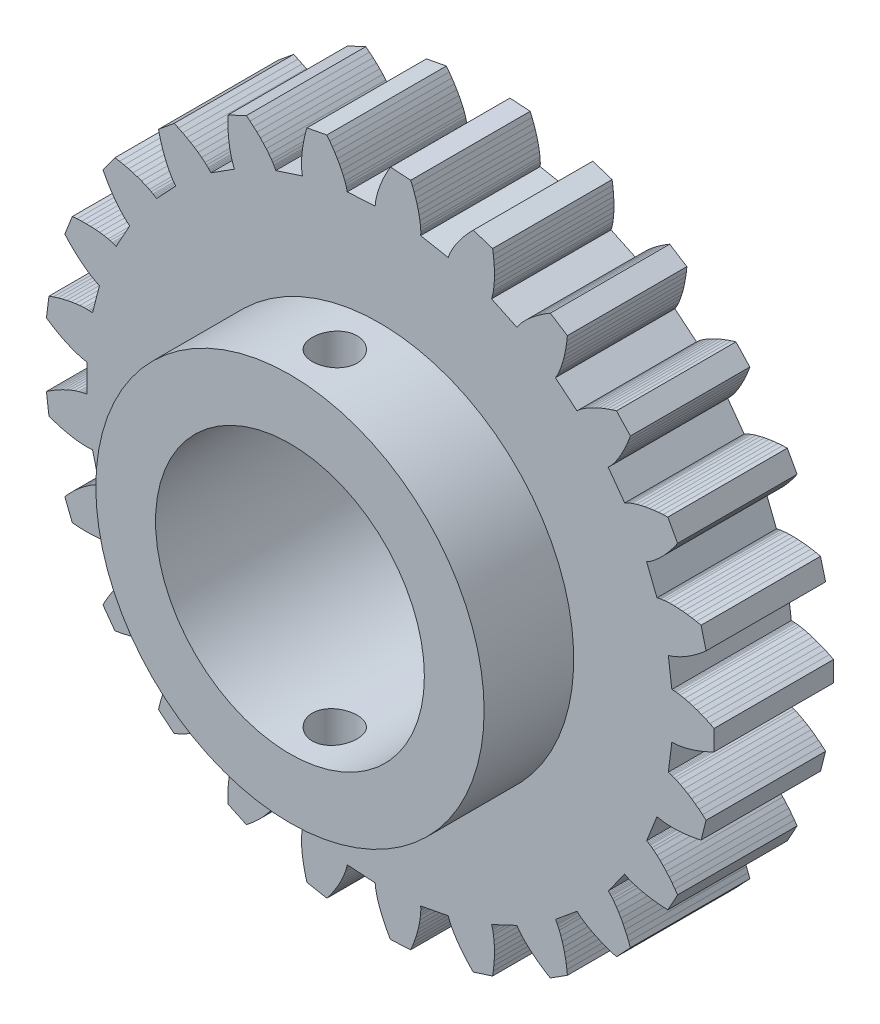
SolidWorks part; units mm, degrees
ref_plane "Front Plane" through (0, 0, 0) normal (0, 0, 1) x (1, 0, 0)
ref_plane "Top Plane" through (0, 0, 0) normal (0, 1, 0) x (1, 0, 0)
ref_plane "Right Plane" through (0, 0, 0) normal (1, 0, 0) x (0, 0, -1)
sketch "Model" plane through (0, 0, 0) normal (0, 0, 1) x (1, 0, 0)
  line L0 (22.5153, 13.4937) -> (22.5501, 13.4944)
  line L1 (22.5501, 13.4944) -> (22.5851, 13.4936)
  line L2 (22.5851, 13.4936) -> (22.6201, 13.4916)
  line L3 (22.6201, 13.4916) -> (22.6552, 13.4888)
  line L4 (22.6552, 13.4888) -> (22.7255, 13.481)
  line L5 (22.7255, 13.481) -> (22.796, 13.4706)
  line L6 (22.796, 13.4706) -> (22.9373, 13.4433)
  line L7 (22.9373, 13.4433) -> (23.079, 13.4085)
  line L8 (23.079, 13.4085) -> (23.221, 13.3669)
  line L9 (23.221, 13.3669) -> (23.363, 13.3191)
  line L10 (23.363, 13.3191) -> (23.5051, 13.2655)
  line L11 (23.5051, 13.2655) -> (23.647, 13.2062)
  line L12 (23.647, 13.2062) -> (23.7888, 13.1416)
  line L13 (23.7888, 13.1416) -> (23.9303, 13.0718)
  line L14 (23.9303, 13.0718) -> (23.9303, 12.3915)
  line L15 (23.9303, 12.3915) -> (23.7888, 12.3217)
  line L16 (23.7888, 12.3217) -> (23.647, 12.257)
  line L17 (23.647, 12.257) -> (23.5051, 12.1978)
  line L18 (23.5051, 12.1978) -> (23.363, 12.1441)
  line L19 (23.363, 12.1441) -> (23.221, 12.0963)
  line L20 (23.221, 12.0963) -> (23.079, 12.0548)
  line L21 (23.079, 12.0548) -> (22.9373, 12.0199)
  line L22 (22.9373, 12.0199) -> (22.796, 11.9927)
  line L23 (22.796, 11.9927) -> (22.7255, 11.9823)
  line L24 (22.7255, 11.9823) -> (22.6552, 11.9745)
  line L25 (22.6552, 11.9745) -> (22.6201, 11.9716)
  line L26 (22.6201, 11.9716) -> (22.5851, 11.9697)
  line L27 (22.5851, 11.9697) -> (22.5501, 11.9688)
  line L28 (22.5501, 11.9688) -> (22.5153, 11.9696)
  line L29 (22.5153, 11.9696) -> (22.3975, 11.0367)
  line L30 (22.3975, 11.0367) -> (22.4314, 11.0287)
  line L31 (22.4314, 11.0287) -> (22.465, 11.0192)
  line L32 (22.465, 11.0192) -> (22.4984, 11.0086)
  line L33 (22.4984, 11.0086) -> (22.5317, 10.9971)
  line L34 (22.5317, 10.9971) -> (22.5978, 10.9721)
  line L35 (22.5978, 10.9721) -> (22.6635, 10.9445)
  line L36 (22.6635, 10.9445) -> (22.7937, 10.8829)
  line L37 (22.7937, 10.8829) -> (22.9223, 10.8139)
  line L38 (22.9223, 10.8139) -> (23.0494, 10.7384)
  line L39 (23.0494, 10.7384) -> (23.1751, 10.6567)
  line L40 (23.1751, 10.6567) -> (23.2994, 10.5694)
  line L41 (23.2994, 10.5694) -> (23.4221, 10.4767)
  line L42 (23.4221, 10.4767) -> (23.5434, 10.3789)
  line L43 (23.5434, 10.3789) -> (23.6631, 10.2761)
  line L44 (23.6631, 10.2761) -> (23.4939, 9.6172)
  line L45 (23.4939, 9.6172) -> (23.3395, 9.5847)
  line L46 (23.3395, 9.5847) -> (23.1861, 9.5574)
  line L47 (23.1861, 9.5574) -> (23.0339, 9.5353)
  line L48 (23.0339, 9.5353) -> (22.8829, 9.5187)
  line L49 (22.8829, 9.5187) -> (22.7334, 9.5077)
  line L50 (22.7334, 9.5077) -> (22.5856, 9.5027)
  line L51 (22.5856, 9.5027) -> (22.4397, 9.5042)
  line L52 (22.4397, 9.5042) -> (22.296, 9.513)
  line L53 (22.296, 9.513) -> (22.2251, 9.5205)
  line L54 (22.2251, 9.5205) -> (22.1551, 9.5304)
  line L55 (22.1551, 9.5304) -> (22.1204, 9.5364)
  line L56 (22.1204, 9.5364) -> (22.086, 9.5432)
  line L57 (22.086, 9.5432) -> (22.0519, 9.551)
  line L58 (22.0519, 9.551) -> (22.0184, 9.5604)
  line L59 (22.0184, 9.5604) -> (21.6723, 8.6861)
  line L60 (21.6723, 8.6861) -> (21.7031, 8.67)
  line L61 (21.7031, 8.67) -> (21.7333, 8.6524)
  line L62 (21.7333, 8.6524) -> (21.7631, 8.6338)
  line L63 (21.7631, 8.6338) -> (21.7925, 8.6145)
  line L64 (21.7925, 8.6145) -> (21.8503, 8.5737)
  line L65 (21.8503, 8.5737) -> (21.9071, 8.5306)
  line L66 (21.9071, 8.5306) -> (22.0178, 8.4387)
  line L67 (22.0178, 8.4387) -> (22.1252, 8.3399)
  line L68 (22.1252, 8.3399) -> (22.2296, 8.2351)
  line L69 (22.2296, 8.2351) -> (22.331, 8.1247)
  line L70 (22.331, 8.1247) -> (22.4297, 8.0093)
  line L71 (22.4297, 8.0093) -> (22.5255, 7.889)
  line L72 (22.5255, 7.889) -> (22.6186, 7.764)
  line L73 (22.6186, 7.764) -> (22.709, 7.6347)
  line L74 (22.709, 7.6347) -> (22.3812, 7.0385)
  line L75 (22.3812, 7.0385) -> (22.2236, 7.0455)
  line L76 (22.2236, 7.0455) -> (22.0683, 7.0572)
  line L77 (22.0683, 7.0572) -> (21.9153, 7.0737)
  line L78 (21.9153, 7.0737) -> (21.765, 7.0951)
  line L79 (21.765, 7.0951) -> (21.6175, 7.1216)
  line L80 (21.6175, 7.1216) -> (21.473, 7.1536)
  line L81 (21.473, 7.1536) -> (21.3321, 7.1913)
  line L82 (21.3321, 7.1913) -> (21.1951, 7.2356)
  line L83 (21.1951, 7.2356) -> (21.1283, 7.2604)
  line L84 (21.1283, 7.2604) -> (21.0629, 7.2874)
  line L85 (21.0629, 7.2874) -> (21.0308, 7.3018)
  line L86 (21.0308, 7.3018) -> (20.9992, 7.317)
  line L87 (20.9992, 7.317) -> (20.9681, 7.3331)
  line L88 (20.9681, 7.3331) -> (20.938, 7.3505)
  line L89 (20.938, 7.3505) -> (20.3853, 6.5898)
  line L90 (20.3853, 6.5898) -> (20.4112, 6.5665)
  line L91 (20.4112, 6.5665) -> (20.4361, 6.5419)
  line L92 (20.4361, 6.5419) -> (20.4602, 6.5165)
  line L93 (20.4602, 6.5165) -> (20.4839, 6.4905)
  line L94 (20.4839, 6.4905) -> (20.5298, 6.4366)
  line L95 (20.5298, 6.4366) -> (20.574, 6.3808)
  line L96 (20.574, 6.3808) -> (20.6584, 6.2642)
  line L97 (20.6584, 6.2642) -> (20.7379, 6.1418)
  line L98 (20.7379, 6.1418) -> (20.8129, 6.0143)
  line L99 (20.8129, 6.0143) -> (20.8838, 5.8822)
  line L100 (20.8838, 5.8822) -> (20.9506, 5.7458)
  line L101 (20.9506, 5.7458) -> (21.0135, 5.6055)
  line L102 (21.0135, 5.6055) -> (21.0726, 5.4613)
  line L103 (21.0726, 5.4613) -> (21.128, 5.3136)
  line L104 (21.128, 5.3136) -> (20.6622, 4.8176)
  line L105 (20.6622, 4.8176) -> (20.5113, 4.8636)
  line L106 (20.5113, 4.8636) -> (20.3638, 4.9136)
  line L107 (20.3638, 4.9136) -> (20.2197, 4.9675)
  line L108 (20.2197, 4.9675) -> (20.0794, 5.0257)
  line L109 (20.0794, 5.0257) -> (19.9432, 5.0881)
  line L110 (19.9432, 5.0881) -> (19.8112, 5.1549)
  line L111 (19.8112, 5.1549) -> (19.6841, 5.2265)
  line L112 (19.6841, 5.2265) -> (19.5624, 5.3035)
  line L113 (19.5624, 5.3035) -> (19.5039, 5.3441)
  line L114 (19.5039, 5.3441) -> (19.4472, 5.3866)
  line L115 (19.4472, 5.3866) -> (19.4197, 5.4085)
  line L116 (19.4197, 5.4085) -> (19.3929, 5.4311)
  line L117 (19.3929, 5.4311) -> (19.3668, 5.4543)
  line L118 (19.3668, 5.4543) -> (19.3419, 5.4787)
  line L119 (19.3419, 5.4787) -> (18.6174, 4.8793)
  line L120 (18.6174, 4.8793) -> (18.6367, 4.8503)
  line L121 (18.6367, 4.8503) -> (18.6547, 4.8204)
  line L122 (18.6547, 4.8204) -> (18.6718, 4.7898)
  line L123 (18.6718, 4.7898) -> (18.6882, 4.7586)
  line L124 (18.6882, 4.7586) -> (18.7193, 4.6951)
  line L125 (18.7193, 4.6951) -> (18.7483, 4.63)
  line L126 (18.7483, 4.63) -> (18.801, 4.496)
  line L127 (18.801, 4.496) -> (18.8476, 4.3577)
  line L128 (18.8476, 4.3577) -> (18.8885, 4.2156)
  line L129 (18.8885, 4.2156) -> (18.9243, 4.07)
  line L130 (18.9243, 4.07) -> (18.9551, 3.9213)
  line L131 (18.9551, 3.9213) -> (18.9811, 3.7697)
  line L132 (18.9811, 3.7697) -> (19.0025, 3.6154)
  line L133 (19.0025, 3.6154) -> (19.0194, 3.4586)
  line L134 (19.0194, 3.4586) -> (18.445, 3.094)
  line L135 (18.445, 3.094) -> (18.3102, 3.1761)
  line L136 (18.3102, 3.1761) -> (18.1797, 3.2611)
  line L137 (18.1797, 3.2611) -> (18.0536, 3.3493)
  line L138 (18.0536, 3.3493) -> (17.9322, 3.4404)
  line L139 (17.9322, 3.4404) -> (17.8157, 3.5348)
  line L140 (17.8157, 3.5348) -> (17.7045, 3.6323)
  line L141 (17.7045, 3.6323) -> (17.5992, 3.7333)
  line L142 (17.5992, 3.7333) -> (17.5004, 3.8381)
  line L143 (17.5004, 3.8381) -> (17.4539, 3.892)
  line L144 (17.4539, 3.892) -> (17.4096, 3.9472)
  line L145 (17.4096, 3.9472) -> (17.3884, 3.9753)
  line L146 (17.3884, 3.9753) -> (17.368, 4.0038)
  line L147 (17.368, 4.0038) -> (17.3486, 4.0329)
  line L148 (17.3486, 4.0329) -> (17.3305, 4.0626)
  line L149 (17.3305, 4.0626) -> (16.4797, 3.6623)
  line L150 (16.4797, 3.6623) -> (16.4912, 3.6294)
  line L151 (16.4912, 3.6294) -> (16.5012, 3.5959)
  line L152 (16.5012, 3.5959) -> (16.5101, 3.562)
  line L153 (16.5101, 3.562) -> (16.5183, 3.5278)
  line L154 (16.5183, 3.5278) -> (16.5326, 3.4585)
  line L155 (16.5326, 3.4585) -> (16.5445, 3.3882)
  line L156 (16.5445, 3.3882) -> (16.5622, 3.2454)
  line L157 (16.5622, 3.2454) -> (16.5729, 3.0998)
  line L158 (16.5729, 3.0998) -> (16.5772, 2.952)
  line L159 (16.5772, 2.952) -> (16.5756, 2.8021)
  line L160 (16.5756, 2.8021) -> (16.5685, 2.6504)
  line L161 (16.5685, 2.6504) -> (16.556, 2.4971)
  line L162 (16.556, 2.4971) -> (16.5384, 2.3423)
  line L163 (16.5384, 2.3423) -> (16.5157, 2.1862)
  line L164 (16.5157, 2.1862) -> (15.8687, 1.9759)
  line L165 (15.8687, 1.9759) -> (15.7586, 2.0889)
  line L166 (15.7586, 2.0889) -> (15.6533, 2.2038)
  line L167 (15.6533, 2.2038) -> (15.5531, 2.3205)
  line L168 (15.5531, 2.3205) -> (15.4582, 2.439)
  line L169 (15.4582, 2.439) -> (15.3688, 2.5593)
  line L170 (15.3688, 2.5593) -> (15.2854, 2.6815)
  line L171 (15.2854, 2.6815) -> (15.2085, 2.8055)
  line L172 (15.2085, 2.8055) -> (15.1389, 2.9315)
  line L173 (15.1389, 2.9315) -> (15.1072, 2.9954)
  line L174 (15.1072, 2.9954) -> (15.078, 3.0598)
  line L175 (15.078, 3.0598) -> (15.0645, 3.0923)
  line L176 (15.0645, 3.0923) -> (15.0519, 3.125)
  line L177 (15.0519, 3.125) -> (15.0402, 3.158)
  line L178 (15.0402, 3.158) -> (15.0302, 3.1913)
  line L179 (15.0302, 3.1913) -> (14.1065, 3.0151)
  line L180 (14.1065, 3.0151) -> (14.1095, 2.9804)
  line L181 (14.1095, 2.9804) -> (14.1108, 2.9455)
  line L182 (14.1108, 2.9455) -> (14.111, 2.9104)
  line L183 (14.111, 2.9104) -> (14.1104, 2.8752)
  line L184 (14.1104, 2.8752) -> (14.107, 2.8046)
  line L185 (14.107, 2.8046) -> (14.1011, 2.7336)
  line L186 (14.1011, 2.7336) -> (14.0827, 2.5908)
  line L187 (14.0827, 2.5908) -> (14.0569, 2.4471)
  line L188 (14.0569, 2.4471) -> (14.0243, 2.3029)
  line L189 (14.0243, 2.3029) -> (13.9855, 2.1581)
  line L190 (13.9855, 2.1581) -> (13.9409, 2.0129)
  line L191 (13.9409, 2.0129) -> (13.8907, 1.8675)
  line L192 (13.8907, 1.8675) -> (13.8351, 1.722)
  line L193 (13.8351, 1.722) -> (13.7743, 1.5764)
  line L194 (13.7743, 1.5764) -> (13.0953, 1.5337)
  line L195 (13.0953, 1.5337) -> (13.0168, 1.6705)
  line L196 (13.0168, 1.6705) -> (12.9434, 1.808)
  line L197 (12.9434, 1.808) -> (12.8753, 1.9459)
  line L198 (12.8753, 1.9459) -> (12.8128, 2.0843)
  line L199 (12.8128, 2.0843) -> (12.7562, 2.2231)
  line L200 (12.7562, 2.2231) -> (12.7058, 2.3621)
  line L201 (12.7058, 2.3621) -> (12.6622, 2.5014)
  line L202 (12.6622, 2.5014) -> (12.6261, 2.6408)
  line L203 (12.6261, 2.6408) -> (12.6113, 2.7105)
  line L204 (12.6113, 2.7105) -> (12.599, 2.7801)
  line L205 (12.599, 2.7801) -> (12.594, 2.815)
  line L206 (12.594, 2.815) -> (12.5899, 2.8498)
  line L207 (12.5899, 2.8498) -> (12.5868, 2.8846)
  line L208 (12.5868, 2.8846) -> (12.5854, 2.9194)
  line L209 (12.5854, 2.9194) -> (11.6469, 2.9784)
  line L210 (11.6469, 2.9784) -> (11.6411, 2.9441)
  line L211 (11.6411, 2.9441) -> (11.6337, 2.91)
  line L212 (11.6337, 2.91) -> (11.6253, 2.8759)
  line L213 (11.6253, 2.8759) -> (11.6159, 2.842)
  line L214 (11.6159, 2.842) -> (11.595, 2.7744)
  line L215 (11.595, 2.7744) -> (11.5716, 2.7071)
  line L216 (11.5716, 2.7071) -> (11.5184, 2.5733)
  line L217 (11.5184, 2.5733) -> (11.4576, 2.4407)
  line L218 (11.4576, 2.4407) -> (11.3902, 2.309)
  line L219 (11.3902, 2.309) -> (11.3166, 2.1784)
  line L220 (11.3166, 2.1784) -> (11.2372, 2.049)
  line L221 (11.2372, 2.049) -> (11.1525, 1.9206)
  line L222 (11.1525, 1.9206) -> (11.0624, 1.7935)
  line L223 (11.0624, 1.7935) -> (10.9673, 1.6676)
  line L224 (10.9673, 1.6676) -> (10.2991, 1.7951)
  line L225 (10.2991, 1.7951) -> (10.257, 1.9471)
  line L226 (10.257, 1.9471) -> (10.2201, 2.0985)
  line L227 (10.2201, 2.0985) -> (10.1885, 2.249)
  line L228 (10.1885, 2.249) -> (10.1624, 2.3986)
  line L229 (10.1624, 2.3986) -> (10.1421, 2.5471)
  line L230 (10.1421, 2.5471) -> (10.1278, 2.6943)
  line L231 (10.1278, 2.6943) -> (10.1202, 2.8401)
  line L232 (10.1202, 2.8401) -> (10.1199, 2.984)
  line L233 (10.1199, 2.984) -> (10.1229, 3.0552)
  line L234 (10.1229, 3.0552) -> (10.1284, 3.1258)
  line L235 (10.1284, 3.1258) -> (10.1322, 3.1607)
  line L236 (10.1322, 3.1607) -> (10.1368, 3.1955)
  line L237 (10.1368, 3.1955) -> (10.1425, 3.23)
  line L238 (10.1425, 3.23) -> (10.1498, 3.264)
  line L239 (10.1498, 3.264) -> (9.2555, 3.5546)
  line L240 (9.2555, 3.5546) -> (9.2413, 3.5228)
  line L241 (9.2413, 3.5228) -> (9.2257, 3.4916)
  line L242 (9.2257, 3.4916) -> (9.209, 3.4607)
  line L243 (9.209, 3.4607) -> (9.1915, 3.4302)
  line L244 (9.1915, 3.4302) -> (9.1545, 3.3699)
  line L245 (9.1545, 3.3699) -> (9.1151, 3.3105)
  line L246 (9.1151, 3.3105) -> (9.0302, 3.1942)
  line L247 (9.0302, 3.1942) -> (8.9384, 3.0808)
  line L248 (8.9384, 3.0808) -> (8.8403, 2.9701)
  line L249 (8.8403, 2.9701) -> (8.7366, 2.8619)
  line L250 (8.7366, 2.8619) -> (8.6275, 2.7562)
  line L251 (8.6275, 2.7562) -> (8.5135, 2.653)
  line L252 (8.5135, 2.653) -> (8.3947, 2.5522)
  line L253 (8.3947, 2.5522) -> (8.2713, 2.4539)
  line L254 (8.2713, 2.4539) -> (7.6557, 2.7436)
  line L255 (7.6557, 2.7436) -> (7.6528, 2.9013)
  line L256 (7.6528, 2.9013) -> (7.6547, 3.0571)
  line L257 (7.6547, 3.0571) -> (7.6615, 3.2108)
  line L258 (7.6615, 3.2108) -> (7.6734, 3.3622)
  line L259 (7.6734, 3.3622) -> (7.6906, 3.5111)
  line L260 (7.6906, 3.5111) -> (7.7135, 3.6572)
  line L261 (7.7135, 3.6572) -> (7.7423, 3.8003)
  line L262 (7.7423, 3.8003) -> (7.7778, 3.9398)
  line L263 (7.7778, 3.9398) -> (7.7984, 4.008)
  line L264 (7.7984, 4.008) -> (7.8213, 4.0749)
  line L265 (7.8213, 4.0749) -> (7.8337, 4.1079)
  line L266 (7.8337, 4.1079) -> (7.8468, 4.1404)
  line L267 (7.8468, 4.1404) -> (7.8609, 4.1724)
  line L268 (7.8609, 4.1724) -> (7.8764, 4.2036)
  line L269 (7.8764, 4.2036) -> (7.0825, 4.7074)
  line L270 (7.0825, 4.7074) -> (7.0608, 4.6801)
  line L271 (7.0608, 4.6801) -> (7.0379, 4.6537)
  line L272 (7.0379, 4.6537) -> (7.0141, 4.628)
  line L273 (7.0141, 4.628) -> (6.9896, 4.6028)
  line L274 (6.9896, 4.6028) -> (6.9387, 4.5536)
  line L275 (6.9387, 4.5536) -> (6.8858, 4.5059)
  line L276 (6.8858, 4.5059) -> (6.7746, 4.4144)
  line L277 (6.7746, 4.4144) -> (6.6575, 4.3274)
  line L278 (6.6575, 4.3274) -> (6.535, 4.2445)
  line L279 (6.535, 4.2445) -> (6.4076, 4.1655)
  line L280 (6.4076, 4.1655) -> (6.2757, 4.0903)
  line L281 (6.2757, 4.0903) -> (6.1395, 4.0186)
  line L282 (6.1395, 4.0186) -> (5.9994, 3.9506)
  line L283 (5.9994, 3.9506) -> (5.8554, 3.8861)
  line L284 (5.8554, 3.8861) -> (5.3312, 4.3197)
  line L285 (5.3312, 4.3197) -> (5.3676, 4.4732)
  line L286 (5.3676, 4.4732) -> (5.4082, 4.6237)
  line L287 (5.4082, 4.6237) -> (5.453, 4.7708)
  line L288 (5.453, 4.7708) -> (5.5022, 4.9145)
  line L289 (5.5022, 4.9145) -> (5.556, 5.0544)
  line L290 (5.556, 5.0544) -> (5.6144, 5.1903)
  line L291 (5.6144, 5.1903) -> (5.6779, 5.3217)
  line L292 (5.6779, 5.3217) -> (5.747, 5.4479)
  line L293 (5.747, 5.4479) -> (5.7839, 5.5089)
  line L294 (5.7839, 5.5089) -> (5.8227, 5.5681)
  line L295 (5.8227, 5.5681) -> (5.8429, 5.5969)
  line L296 (5.8429, 5.5969) -> (5.8637, 5.6251)
  line L297 (5.8637, 5.6251) -> (5.8853, 5.6526)
  line L298 (5.8853, 5.6526) -> (5.9081, 5.6789)
  line L299 (5.9081, 5.6789) -> (5.2644, 6.3644)
  line L300 (5.2644, 6.3644) -> (5.2367, 6.3433)
  line L301 (5.2367, 6.3433) -> (5.2079, 6.3235)
  line L302 (5.2079, 6.3235) -> (5.1784, 6.3045)
  line L303 (5.1784, 6.3045) -> (5.1484, 6.2862)
  line L304 (5.1484, 6.2862) -> (5.0869, 6.2512)
  line L305 (5.0869, 6.2512) -> (5.0238, 6.2181)
  line L306 (5.0238, 6.2181) -> (4.8934, 6.1571)
  line L307 (4.8934, 6.1571) -> (4.7583, 6.102)
  line L308 (4.7583, 6.102) -> (4.619, 6.0522)
  line L309 (4.619, 6.0522) -> (4.476, 6.0074)
  line L310 (4.476, 6.0074) -> (4.3295, 5.9673)
  line L311 (4.3295, 5.9673) -> (4.1798, 5.9318)
  line L312 (4.1798, 5.9318) -> (4.0272, 5.9007)
  line L313 (4.0272, 5.9007) -> (3.8717, 5.874)
  line L314 (3.8717, 5.874) -> (3.4718, 6.4244)
  line L315 (3.4718, 6.4244) -> (3.5452, 6.5641)
  line L316 (3.5452, 6.5641) -> (3.6219, 6.6996)
  line L317 (3.6219, 6.6996) -> (3.7019, 6.831)
  line L318 (3.7019, 6.831) -> (3.7853, 6.9579)
  line L319 (3.7853, 6.9579) -> (3.8721, 7.0801)
  line L320 (3.8721, 7.0801) -> (3.9625, 7.1972)
  line L321 (3.9625, 7.1972) -> (4.0567, 7.3086)
  line L322 (4.0567, 7.3086) -> (4.1551, 7.4138)
  line L323 (4.1551, 7.4138) -> (4.206, 7.4636)
  line L324 (4.206, 7.4636) -> (4.2583, 7.5113)
  line L325 (4.2583, 7.5113) -> (4.285, 7.5342)
  line L326 (4.285, 7.5342) -> (4.3122, 7.5563)
  line L327 (4.3122, 7.5563) -> (4.3399, 7.5776)
  line L328 (4.3399, 7.5776) -> (4.3685, 7.5975)
  line L329 (4.3685, 7.5975) -> (3.9155, 8.4215)
  line L330 (3.9155, 8.4215) -> (3.8834, 8.4079)
  line L331 (3.8834, 8.4079) -> (3.8506, 8.3959)
  line L332 (3.8506, 8.3959) -> (3.8174, 8.3848)
  line L333 (3.8174, 8.3848) -> (3.7837, 8.3745)
  line L334 (3.7837, 8.3745) -> (3.7154, 8.3559)
  line L335 (3.7154, 8.3559) -> (3.6461, 8.3396)
  line L336 (3.6461, 8.3396) -> (3.5046, 8.3129)
  line L337 (3.5046, 8.3129) -> (3.36, 8.2932)
  line L338 (3.36, 8.2932) -> (3.2127, 8.2796)
  line L339 (3.2127, 8.2796) -> (3.0631, 8.2717)
  line L340 (3.0631, 8.2717) -> (2.9112, 8.2693)
  line L341 (2.9112, 8.2693) -> (2.7574, 8.2721)
  line L342 (2.7574, 8.2721) -> (2.6018, 8.28)
  line L343 (2.6018, 8.28) -> (2.4446, 8.2928)
  line L344 (2.4446, 8.2928) -> (2.1941, 8.9254)
  line L345 (2.1941, 8.9254) -> (2.3, 9.0424)
  line L346 (2.3, 9.0424) -> (2.408, 9.1547)
  line L347 (2.408, 9.1547) -> (2.5182, 9.262)
  line L348 (2.5182, 9.262) -> (2.6305, 9.3642)
  line L349 (2.6305, 9.3642) -> (2.745, 9.4609)
  line L350 (2.745, 9.4609) -> (2.8617, 9.5518)
  line L351 (2.8617, 9.5518) -> (2.9806, 9.6364)
  line L352 (2.9806, 9.6364) -> (3.102, 9.7138)
  line L353 (3.102, 9.7138) -> (3.1637, 9.7494)
  line L354 (3.1637, 9.7494) -> (3.2262, 9.7825)
  line L355 (3.2262, 9.7825) -> (3.2578, 9.7981)
  line L356 (3.2578, 9.7981) -> (3.2897, 9.8128)
  line L357 (3.2897, 9.8128) -> (3.3218, 9.8265)
  line L358 (3.3218, 9.8265) -> (3.3544, 9.8386)
  line L359 (3.3544, 9.8386) -> (3.1206, 10.7493)
  line L360 (3.1206, 10.7493) -> (3.0862, 10.7442)
  line L361 (3.0862, 10.7442) -> (3.0514, 10.7407)
  line L362 (3.0514, 10.7407) -> (3.0164, 10.7383)
  line L363 (3.0164, 10.7383) -> (2.9813, 10.7367)
  line L364 (2.9813, 10.7367) -> (2.9105, 10.7356)
  line L365 (2.9105, 10.7356) -> (2.8393, 10.7371)
  line L366 (2.8393, 10.7371) -> (2.6956, 10.7464)
  line L367 (2.6956, 10.7464) -> (2.5506, 10.7632)
  line L368 (2.5506, 10.7632) -> (2.4046, 10.7867)
  line L369 (2.4046, 10.7867) -> (2.2577, 10.8163)
  line L370 (2.2577, 10.8163) -> (2.11, 10.8517)
  line L371 (2.11, 10.8517) -> (1.9618, 10.8927)
  line L372 (1.9618, 10.8927) -> (1.813, 10.9391)
  line L373 (1.813, 10.9391) -> (1.6639, 10.9906)
  line L374 (1.6639, 10.9906) -> (1.5786, 11.6655)
  line L375 (1.5786, 11.6655) -> (1.7103, 11.7525)
  line L376 (1.7103, 11.7525) -> (1.8428, 11.8344)
  line L377 (1.8428, 11.8344) -> (1.9762, 11.911)
  line L378 (1.9762, 11.911) -> (2.1104, 11.982)
  line L379 (2.1104, 11.982) -> (2.2454, 12.0472)
  line L380 (2.2454, 12.0472) -> (2.381, 12.1063)
  line L381 (2.381, 12.1063) -> (2.5172, 12.1586)
  line L382 (2.5172, 12.1586) -> (2.654, 12.2034)
  line L383 (2.654, 12.2034) -> (2.7227, 12.2225)
  line L384 (2.7227, 12.2225) -> (2.7915, 12.2391)
  line L385 (2.7915, 12.2391) -> (2.8259, 12.2463)
  line L386 (2.8259, 12.2463) -> (2.8604, 12.2526)
  line L387 (2.8604, 12.2526) -> (2.8949, 12.2578)
  line L388 (2.8949, 12.2578) -> (2.9296, 12.2615)
  line L389 (2.9296, 12.2615) -> (2.9296, 13.2018)
  line L390 (2.9296, 13.2018) -> (2.8949, 13.2054)
  line L391 (2.8949, 13.2054) -> (2.8604, 13.2107)
  line L392 (2.8604, 13.2107) -> (2.8259, 13.217)
  line L393 (2.8259, 13.217) -> (2.7915, 13.2242)
  line L394 (2.7915, 13.2242) -> (2.7227, 13.2408)
  line L395 (2.7227, 13.2408) -> (2.654, 13.2599)
  line L396 (2.654, 13.2599) -> (2.5172, 13.3047)
  line L397 (2.5172, 13.3047) -> (2.381, 13.357)
  line L398 (2.381, 13.357) -> (2.2454, 13.416)
  line L399 (2.2454, 13.416) -> (2.1104, 13.4812)
  line L400 (2.1104, 13.4812) -> (1.9762, 13.5523)
  line L401 (1.9762, 13.5523) -> (1.8428, 13.6289)
  line L402 (1.8428, 13.6289) -> (1.7103, 13.7107)
  line L403 (1.7103, 13.7107) -> (1.5786, 13.7977)
  line L404 (1.5786, 13.7977) -> (1.6639, 14.4727)
  line L405 (1.6639, 14.4727) -> (1.813, 14.5242)
  line L406 (1.813, 14.5242) -> (1.9618, 14.5705)
  line L407 (1.9618, 14.5705) -> (2.11, 14.6115)
  line L408 (2.11, 14.6115) -> (2.2577, 14.647)
  line L409 (2.2577, 14.647) -> (2.4046, 14.6766)
  line L410 (2.4046, 14.6766) -> (2.5506, 14.7)
  line L411 (2.5506, 14.7) -> (2.6956, 14.7168)
  line L412 (2.6956, 14.7168) -> (2.8393, 14.7261)
  line L413 (2.8393, 14.7261) -> (2.9105, 14.7276)
  line L414 (2.9105, 14.7276) -> (2.9813, 14.7266)
  line L415 (2.9813, 14.7266) -> (3.0164, 14.725)
  line L416 (3.0164, 14.725) -> (3.0514, 14.7225)
  line L417 (3.0514, 14.7225) -> (3.0862, 14.719)
  line L418 (3.0862, 14.719) -> (3.1206, 14.7139)
  line L419 (3.1206, 14.7139) -> (3.3544, 15.6247)
  line L420 (3.3544, 15.6247) -> (3.3218, 15.6368)
  line L421 (3.3218, 15.6368) -> (3.2897, 15.6505)
  line L422 (3.2897, 15.6505) -> (3.2578, 15.6652)
  line L423 (3.2578, 15.6652) -> (3.2262, 15.6807)
  line L424 (3.2262, 15.6807) -> (3.1637, 15.7139)
  line L425 (3.1637, 15.7139) -> (3.102, 15.7495)
  line L426 (3.102, 15.7495) -> (2.9806, 15.8269)
  line L427 (2.9806, 15.8269) -> (2.8617, 15.9114)
  line L428 (2.8617, 15.9114) -> (2.745, 16.0023)
  line L429 (2.745, 16.0023) -> (2.6305, 16.0991)
  line L430 (2.6305, 16.0991) -> (2.5182, 16.2013)
  line L431 (2.5182, 16.2013) -> (2.408, 16.3086)
  line L432 (2.408, 16.3086) -> (2.3, 16.4209)
  line L433 (2.3, 16.4209) -> (2.1941, 16.5379)
  line L434 (2.1941, 16.5379) -> (2.4446, 17.1704)
  line L435 (2.4446, 17.1704) -> (2.6018, 17.1832)
  line L436 (2.6018, 17.1832) -> (2.7574, 17.1911)
  line L437 (2.7574, 17.1911) -> (2.9112, 17.1939)
  line L438 (2.9112, 17.1939) -> (3.0631, 17.1915)
  line L439 (3.0631, 17.1915) -> (3.2127, 17.1837)
  line L440 (3.2127, 17.1837) -> (3.36, 17.1701)
  line L441 (3.36, 17.1701) -> (3.5046, 17.1503)
  line L442 (3.5046, 17.1503) -> (3.6461, 17.1236)
  line L443 (3.6461, 17.1236) -> (3.7154, 17.1073)
  line L444 (3.7154, 17.1073) -> (3.7837, 17.0887)
  line L445 (3.7837, 17.0887) -> (3.8174, 17.0784)
  line L446 (3.8174, 17.0784) -> (3.8506, 17.0674)
  line L447 (3.8506, 17.0674) -> (3.8834, 17.0553)
  line L448 (3.8834, 17.0553) -> (3.9155, 17.0418)
  line L449 (3.9155, 17.0418) -> (4.3685, 17.8658)
  line L450 (4.3685, 17.8658) -> (4.3399, 17.8857)
  line L451 (4.3399, 17.8857) -> (4.3122, 17.9069)
  line L452 (4.3122, 17.9069) -> (4.285, 17.9291)
  line L453 (4.285, 17.9291) -> (4.2583, 17.952)
  line L454 (4.2583, 17.952) -> (4.206, 17.9996)
  line L455 (4.206, 17.9996) -> (4.1551, 18.0495)
  line L456 (4.1551, 18.0495) -> (4.0567, 18.1546)
  line L457 (4.0567, 18.1546) -> (3.9625, 18.2661)
  line L458 (3.9625, 18.2661) -> (3.8721, 18.3831)
  line L459 (3.8721, 18.3831) -> (3.7853, 18.5053)
  line L460 (3.7853, 18.5053) -> (3.7019, 18.6322)
  line L461 (3.7019, 18.6322) -> (3.6219, 18.7636)
  line L462 (3.6219, 18.7636) -> (3.5452, 18.8992)
  line L463 (3.5452, 18.8992) -> (3.4718, 19.0388)
  line L464 (3.4718, 19.0388) -> (3.8717, 19.5892)
  line L465 (3.8717, 19.5892) -> (4.0272, 19.5626)
  line L466 (4.0272, 19.5626) -> (4.1798, 19.5315)
  line L467 (4.1798, 19.5315) -> (4.3295, 19.496)
  line L468 (4.3295, 19.496) -> (4.476, 19.4559)
  line L469 (4.476, 19.4559) -> (4.619, 19.4111)
  line L470 (4.619, 19.4111) -> (4.7583, 19.3613)
  line L471 (4.7583, 19.3613) -> (4.8934, 19.3062)
  line L472 (4.8934, 19.3062) -> (5.0238, 19.2451)
  line L473 (5.0238, 19.2451) -> (5.0869, 19.2121)
  line L474 (5.0869, 19.2121) -> (5.1484, 19.1771)
  line L475 (5.1484, 19.1771) -> (5.1784, 19.1588)
  line L476 (5.1784, 19.1588) -> (5.2079, 19.1398)
  line L477 (5.2079, 19.1398) -> (5.2367, 19.1199)
  line L478 (5.2367, 19.1199) -> (5.2644, 19.0989)
  line L479 (5.2644, 19.0989) -> (5.9081, 19.7843)
  line L480 (5.9081, 19.7843) -> (5.8853, 19.8107)
  line L481 (5.8853, 19.8107) -> (5.8637, 19.8381)
  line L482 (5.8637, 19.8381) -> (5.8429, 19.8664)
  line L483 (5.8429, 19.8664) -> (5.8227, 19.8952)
  line L484 (5.8227, 19.8952) -> (5.7839, 19.9544)
  line L485 (5.7839, 19.9544) -> (5.747, 20.0153)
  line L486 (5.747, 20.0153) -> (5.6779, 20.1416)
  line L487 (5.6779, 20.1416) -> (5.6144, 20.273)
  line L488 (5.6144, 20.273) -> (5.556, 20.4089)
  line L489 (5.556, 20.4089) -> (5.5022, 20.5488)
  line L490 (5.5022, 20.5488) -> (5.453, 20.6925)
  line L491 (5.453, 20.6925) -> (5.4082, 20.8396)
  line L492 (5.4082, 20.8396) -> (5.3676, 20.99)
  line L493 (5.3676, 20.99) -> (5.3312, 21.1435)
  line L494 (5.3312, 21.1435) -> (5.8554, 21.5772)
  line L495 (5.8554, 21.5772) -> (5.9994, 21.5127)
  line L496 (5.9994, 21.5127) -> (6.1395, 21.4446)
  line L497 (6.1395, 21.4446) -> (6.2757, 21.373)
  line L498 (6.2757, 21.373) -> (6.4076, 21.2977)
  line L499 (6.4076, 21.2977) -> (6.535, 21.2188)
  line L500 (6.535, 21.2188) -> (6.6575, 21.1359)
  line L501 (6.6575, 21.1359) -> (6.7746, 21.0489)
  line L502 (6.7746, 21.0489) -> (6.8858, 20.9574)
  line L503 (6.8858, 20.9574) -> (6.9387, 20.9097)
  line L504 (6.9387, 20.9097) -> (6.9896, 20.8605)
  line L505 (6.9896, 20.8605) -> (7.0141, 20.8352)
  line L506 (7.0141, 20.8352) -> (7.0379, 20.8095)
  line L507 (7.0379, 20.8095) -> (7.0608, 20.7831)
  line L508 (7.0608, 20.7831) -> (7.0825, 20.7559)
  line L509 (7.0825, 20.7559) -> (7.8764, 21.2597)
  line L510 (7.8764, 21.2597) -> (7.8609, 21.2909)
  line L511 (7.8609, 21.2909) -> (7.8468, 21.3229)
  line L512 (7.8468, 21.3229) -> (7.8337, 21.3554)
  line L513 (7.8337, 21.3554) -> (7.8213, 21.3883)
  line L514 (7.8213, 21.3883) -> (7.7984, 21.4553)
  line L515 (7.7984, 21.4553) -> (7.7778, 21.5235)
  line L516 (7.7778, 21.5235) -> (7.7423, 21.663)
  line L517 (7.7423, 21.663) -> (7.7135, 21.806)
  line L518 (7.7135, 21.806) -> (7.6906, 21.9522)
  line L519 (7.6906, 21.9522) -> (7.6734, 22.1011)
  line L520 (7.6734, 22.1011) -> (7.6615, 22.2525)
  line L521 (7.6615, 22.2525) -> (7.6547, 22.4061)
  line L522 (7.6547, 22.4061) -> (7.6528, 22.5619)
  line L523 (7.6528, 22.5619) -> (7.6557, 22.7196)
  line L524 (7.6557, 22.7196) -> (8.2713, 23.0093)
  line L525 (8.2713, 23.0093) -> (8.3947, 22.911)
  line L526 (8.3947, 22.911) -> (8.5135, 22.8103)
  line L527 (8.5135, 22.8103) -> (8.6275, 22.707)
  line L528 (8.6275, 22.707) -> (8.7366, 22.6013)
  line L529 (8.7366, 22.6013) -> (8.8403, 22.4932)
  line L530 (8.8403, 22.4932) -> (8.9384, 22.3824)
  line L531 (8.9384, 22.3824) -> (9.0302, 22.269)
  line L532 (9.0302, 22.269) -> (9.1151, 22.1527)
  line L533 (9.1151, 22.1527) -> (9.1545, 22.0934)
  line L534 (9.1545, 22.0934) -> (9.1915, 22.0331)
  line L535 (9.1915, 22.0331) -> (9.209, 22.0026)
  line L536 (9.209, 22.0026) -> (9.2257, 21.9717)
  line L537 (9.2257, 21.9717) -> (9.2413, 21.9405)
  line L538 (9.2413, 21.9405) -> (9.2555, 21.9086)
  line L539 (9.2555, 21.9086) -> (10.1498, 22.1992)
  line L540 (10.1498, 22.1992) -> (10.1425, 22.2333)
  line L541 (10.1425, 22.2333) -> (10.1368, 22.2677)
  line L542 (10.1368, 22.2677) -> (10.1322, 22.3025)
  line L543 (10.1322, 22.3025) -> (10.1284, 22.3375)
  line L544 (10.1284, 22.3375) -> (10.1229, 22.408)
  line L545 (10.1229, 22.408) -> (10.1199, 22.4792)
  line L546 (10.1199, 22.4792) -> (10.1202, 22.6232)
  line L547 (10.1202, 22.6232) -> (10.1278, 22.7689)
  line L548 (10.1278, 22.7689) -> (10.1421, 22.9161)
  line L549 (10.1421, 22.9161) -> (10.1624, 23.0646)
  line L550 (10.1624, 23.0646) -> (10.1885, 23.2142)
  line L551 (10.1885, 23.2142) -> (10.2201, 23.3648)
  line L552 (10.2201, 23.3648) -> (10.257, 23.5161)
  line L553 (10.257, 23.5161) -> (10.2991, 23.6682)
  line L554 (10.2991, 23.6682) -> (10.9673, 23.7957)
  line L555 (10.9673, 23.7957) -> (11.0624, 23.6698)
  line L556 (11.0624, 23.6698) -> (11.1525, 23.5426)
  line L557 (11.1525, 23.5426) -> (11.2372, 23.4143)
  line L558 (11.2372, 23.4143) -> (11.3166, 23.2848)
  line L559 (11.3166, 23.2848) -> (11.3902, 23.1542)
  line L560 (11.3902, 23.1542) -> (11.4576, 23.0226)
  line L561 (11.4576, 23.0226) -> (11.5184, 22.8899)
  line L562 (11.5184, 22.8899) -> (11.5716, 22.7562)
  line L563 (11.5716, 22.7562) -> (11.595, 22.6889)
  line L564 (11.595, 22.6889) -> (11.6159, 22.6213)
  line L565 (11.6159, 22.6213) -> (11.6253, 22.5873)
  line L566 (11.6253, 22.5873) -> (11.6337, 22.5533)
  line L567 (11.6337, 22.5533) -> (11.6411, 22.5191)
  line L568 (11.6411, 22.5191) -> (11.6469, 22.4848)
  line L569 (11.6469, 22.4848) -> (12.5854, 22.5439)
  line L570 (12.5854, 22.5439) -> (12.5868, 22.5786)
  line L571 (12.5868, 22.5786) -> (12.5899, 22.6135)
  line L572 (12.5899, 22.6135) -> (12.594, 22.6483)
  line L573 (12.594, 22.6483) -> (12.599, 22.6831)
  line L574 (12.599, 22.6831) -> (12.6113, 22.7528)
  line L575 (12.6113, 22.7528) -> (12.6261, 22.8225)
  line L576 (12.6261, 22.8225) -> (12.6622, 22.9619)
  line L577 (12.6622, 22.9619) -> (12.7058, 23.1011)
  line L578 (12.7058, 23.1011) -> (12.7562, 23.2402)
  line L579 (12.7562, 23.2402) -> (12.8128, 23.3789)
  line L580 (12.8128, 23.3789) -> (12.8753, 23.5174)
  line L581 (12.8753, 23.5174) -> (12.9434, 23.6553)
  line L582 (12.9434, 23.6553) -> (13.0168, 23.7927)
  line L583 (13.0168, 23.7927) -> (13.0953, 23.9296)
  line L584 (13.0953, 23.9296) -> (13.7743, 23.8868)
  line L585 (13.7743, 23.8868) -> (13.8351, 23.7412)
  line L586 (13.8351, 23.7412) -> (13.8907, 23.5957)
  line L587 (13.8907, 23.5957) -> (13.9409, 23.4503)
  line L588 (13.9409, 23.4503) -> (13.9855, 23.3052)
  line L589 (13.9855, 23.3052) -> (14.0243, 23.1604)
  line L590 (14.0243, 23.1604) -> (14.0569, 23.0161)
  line L591 (14.0569, 23.0161) -> (14.0827, 22.8725)
  line L592 (14.0827, 22.8725) -> (14.1011, 22.7297)
  line L593 (14.1011, 22.7297) -> (14.107, 22.6587)
  line L594 (14.107, 22.6587) -> (14.1104, 22.588)
  line L595 (14.1104, 22.588) -> (14.111, 22.5528)
  line L596 (14.111, 22.5528) -> (14.1108, 22.5178)
  line L597 (14.1108, 22.5178) -> (14.1095, 22.4828)
  line L598 (14.1095, 22.4828) -> (14.1065, 22.4482)
  line L599 (14.1065, 22.4482) -> (15.0302, 22.272)
  line L600 (15.0302, 22.272) -> (15.0402, 22.3053)
  line L601 (15.0402, 22.3053) -> (15.0519, 22.3382)
  line L602 (15.0519, 22.3382) -> (15.0645, 22.3709)
  line L603 (15.0645, 22.3709) -> (15.078, 22.4034)
  line L604 (15.078, 22.4034) -> (15.1072, 22.4679)
  line L605 (15.1072, 22.4679) -> (15.1389, 22.5317)
  line L606 (15.1389, 22.5317) -> (15.2085, 22.6577)
  line L607 (15.2085, 22.6577) -> (15.2854, 22.7818)
  line L608 (15.2854, 22.7818) -> (15.3688, 22.9039)
  line L609 (15.3688, 22.9039) -> (15.4582, 23.0242)
  line L610 (15.4582, 23.0242) -> (15.5531, 23.1428)
  line L611 (15.5531, 23.1428) -> (15.6533, 23.2595)
  line L612 (15.6533, 23.2595) -> (15.7586, 23.3743)
  line L613 (15.7586, 23.3743) -> (15.8687, 23.4873)
  line L614 (15.8687, 23.4873) -> (16.5157, 23.2771)
  line L615 (16.5157, 23.2771) -> (16.5384, 23.1209)
  line L616 (16.5384, 23.1209) -> (16.556, 22.9662)
  line L617 (16.556, 22.9662) -> (16.5685, 22.8128)
  line L618 (16.5685, 22.8128) -> (16.5756, 22.6612)
  line L619 (16.5756, 22.6612) -> (16.5772, 22.5113)
  line L620 (16.5772, 22.5113) -> (16.5729, 22.3634)
  line L621 (16.5729, 22.3634) -> (16.5622, 22.2179)
  line L622 (16.5622, 22.2179) -> (16.5445, 22.075)
  line L623 (16.5445, 22.075) -> (16.5326, 22.0048)
  line L624 (16.5326, 22.0048) -> (16.5183, 21.9355)
  line L625 (16.5183, 21.9355) -> (16.5101, 21.9012)
  line L626 (16.5101, 21.9012) -> (16.5012, 21.8673)
  line L627 (16.5012, 21.8673) -> (16.4912, 21.8338)
  line L628 (16.4912, 21.8338) -> (16.4797, 21.801)
  line L629 (16.4797, 21.801) -> (17.3305, 21.4006)
  line L630 (17.3305, 21.4006) -> (17.3486, 21.4304)
  line L631 (17.3486, 21.4304) -> (17.368, 21.4594)
  line L632 (17.368, 21.4594) -> (17.3884, 21.4879)
  line L633 (17.3884, 21.4879) -> (17.4096, 21.5161)
  line L634 (17.4096, 21.5161) -> (17.4539, 21.5712)
  line L635 (17.4539, 21.5712) -> (17.5004, 21.6252)
  line L636 (17.5004, 21.6252) -> (17.5992, 21.7299)
  line L637 (17.5992, 21.7299) -> (17.7045, 21.8309)
  line L638 (17.7045, 21.8309) -> (17.8157, 21.9285)
  line L639 (17.8157, 21.9285) -> (17.9322, 22.0228)
  line L640 (17.9322, 22.0228) -> (18.0536, 22.114)
  line L641 (18.0536, 22.114) -> (18.1797, 22.2021)
  line L642 (18.1797, 22.2021) -> (18.3102, 22.2872)
  line L643 (18.3102, 22.2872) -> (18.445, 22.3692)
  line L644 (18.445, 22.3692) -> (19.0194, 22.0047)
  line L645 (19.0194, 22.0047) -> (19.0025, 21.8478)
  line L646 (19.0025, 21.8478) -> (18.9811, 21.6935)
  line L647 (18.9811, 21.6935) -> (18.9551, 21.5419)
  line L648 (18.9551, 21.5419) -> (18.9243, 21.3932)
  line L649 (18.9243, 21.3932) -> (18.8885, 21.2477)
  line L650 (18.8885, 21.2477) -> (18.8476, 21.1055)
  line L651 (18.8476, 21.1055) -> (18.801, 20.9672)
  line L652 (18.801, 20.9672) -> (18.7483, 20.8333)
  line L653 (18.7483, 20.8333) -> (18.7193, 20.7682)
  line L654 (18.7193, 20.7682) -> (18.6882, 20.7046)
  line L655 (18.6882, 20.7046) -> (18.6718, 20.6735)
  line L656 (18.6718, 20.6735) -> (18.6547, 20.6429)
  line L657 (18.6547, 20.6429) -> (18.6367, 20.6129)
  line L658 (18.6367, 20.6129) -> (18.6174, 20.5839)
  line L659 (18.6174, 20.5839) -> (19.3419, 19.9846)
  line L660 (19.3419, 19.9846) -> (19.3668, 20.0089)
  line L661 (19.3668, 20.0089) -> (19.3929, 20.0322)
  line L662 (19.3929, 20.0322) -> (19.4197, 20.0547)
  line L663 (19.4197, 20.0547) -> (19.4472, 20.0767)
  line L664 (19.4472, 20.0767) -> (19.5039, 20.1191)
  line L665 (19.5039, 20.1191) -> (19.5624, 20.1598)
  line L666 (19.5624, 20.1598) -> (19.6841, 20.2367)
  line L667 (19.6841, 20.2367) -> (19.8112, 20.3083)
  line L668 (19.8112, 20.3083) -> (19.9432, 20.3752)
  line L669 (19.9432, 20.3752) -> (20.0794, 20.4376)
  line L670 (20.0794, 20.4376) -> (20.2197, 20.4957)
  line L671 (20.2197, 20.4957) -> (20.3638, 20.5497)
  line L672 (20.3638, 20.5497) -> (20.5113, 20.5996)
  line L673 (20.5113, 20.5996) -> (20.6622, 20.6456)
  line L674 (20.6622, 20.6456) -> (21.128, 20.1497)
  line L675 (21.128, 20.1497) -> (21.0726, 20.0019)
  line L676 (21.0726, 20.0019) -> (21.0135, 19.8578)
  line L677 (21.0135, 19.8578) -> (20.9506, 19.7174)
  line L678 (20.9506, 19.7174) -> (20.8838, 19.5811)
  line L679 (20.8838, 19.5811) -> (20.8129, 19.449)
  line L680 (20.8129, 19.449) -> (20.7379, 19.3215)
  line L681 (20.7379, 19.3215) -> (20.6584, 19.1991)
  line L682 (20.6584, 19.1991) -> (20.574, 19.0825)
  line L683 (20.574, 19.0825) -> (20.5298, 19.0266)
  line L684 (20.5298, 19.0266) -> (20.4839, 18.9728)
  line L685 (20.4839, 18.9728) -> (20.4602, 18.9467)
  line L686 (20.4602, 18.9467) -> (20.4361, 18.9213)
  line L687 (20.4361, 18.9213) -> (20.4112, 18.8968)
  line L688 (20.4112, 18.8968) -> (20.3853, 18.8735)
  line L689 (20.3853, 18.8735) -> (20.938, 18.1128)
  line L690 (20.938, 18.1128) -> (20.9681, 18.1302)
  line L691 (20.9681, 18.1302) -> (20.9992, 18.1462)
  line L692 (20.9992, 18.1462) -> (21.0308, 18.1614)
  line L693 (21.0308, 18.1614) -> (21.0629, 18.1758)
  line L694 (21.0629, 18.1758) -> (21.1283, 18.2028)
  line L695 (21.1283, 18.2028) -> (21.1951, 18.2277)
  line L696 (21.1951, 18.2277) -> (21.3321, 18.2719)
  line L697 (21.3321, 18.2719) -> (21.473, 18.3097)
  line L698 (21.473, 18.3097) -> (21.6175, 18.3416)
  line L699 (21.6175, 18.3416) -> (21.765, 18.3682)
  line L700 (21.765, 18.3682) -> (21.9153, 18.3896)
  line L701 (21.9153, 18.3896) -> (22.0683, 18.406)
  line L702 (22.0683, 18.406) -> (22.2236, 18.4177)
  line L703 (22.2236, 18.4177) -> (22.3812, 18.4247)
  line L704 (22.3812, 18.4247) -> (22.709, 17.8285)
  line L705 (22.709, 17.8285) -> (22.6186, 17.6992)
  line L706 (22.6186, 17.6992) -> (22.5255, 17.5743)
  line L707 (22.5255, 17.5743) -> (22.4297, 17.454)
  line L708 (22.4297, 17.454) -> (22.331, 17.3385)
  line L709 (22.331, 17.3385) -> (22.2296, 17.2282)
  line L710 (22.2296, 17.2282) -> (22.1252, 17.1234)
  line L711 (22.1252, 17.1234) -> (22.0178, 17.0246)
  line L712 (22.0178, 17.0246) -> (21.9071, 16.9326)
  line L713 (21.9071, 16.9326) -> (21.8503, 16.8896)
  line L714 (21.8503, 16.8896) -> (21.7925, 16.8488)
  line L715 (21.7925, 16.8488) -> (21.7631, 16.8294)
  line L716 (21.7631, 16.8294) -> (21.7333, 16.8109)
  line L717 (21.7333, 16.8109) -> (21.7031, 16.7933)
  line L718 (21.7031, 16.7933) -> (21.6723, 16.7771)
  line L719 (21.6723, 16.7771) -> (22.0184, 15.9029)
  line L720 (22.0184, 15.9029) -> (22.0519, 15.9122)
  line L721 (22.0519, 15.9122) -> (22.086, 15.9201)
  line L722 (22.086, 15.9201) -> (22.1204, 15.9269)
  line L723 (22.1204, 15.9269) -> (22.1551, 15.9329)
  line L724 (22.1551, 15.9329) -> (22.2251, 15.9428)
  line L725 (22.2251, 15.9428) -> (22.296, 15.9503)
  line L726 (22.296, 15.9503) -> (22.4397, 15.959)
  line L727 (22.4397, 15.959) -> (22.5856, 15.9605)
  line L728 (22.5856, 15.9605) -> (22.7334, 15.9556)
  line L729 (22.7334, 15.9556) -> (22.8829, 15.9446)
  line L730 (22.8829, 15.9446) -> (23.0339, 15.9279)
  line L731 (23.0339, 15.9279) -> (23.1861, 15.9059)
  line L732 (23.1861, 15.9059) -> (23.3395, 15.8785)
  line L733 (23.3395, 15.8785) -> (23.4939, 15.8461)
  line L734 (23.4939, 15.8461) -> (23.6631, 15.1871)
  line L735 (23.6631, 15.1871) -> (23.5434, 15.0844)
  line L736 (23.5434, 15.0844) -> (23.4221, 14.9865)
  line L737 (23.4221, 14.9865) -> (23.2994, 14.8938)
  line L738 (23.2994, 14.8938) -> (23.1751, 14.8065)
  line L739 (23.1751, 14.8065) -> (23.0494, 14.7249)
  line L740 (23.0494, 14.7249) -> (22.9223, 14.6493)
  line L741 (22.9223, 14.6493) -> (22.7937, 14.5803)
  line L742 (22.7937, 14.5803) -> (22.6635, 14.5188)
  line L743 (22.6635, 14.5188) -> (22.5978, 14.4912)
  line L744 (22.5978, 14.4912) -> (22.5317, 14.4661)
  line L745 (22.5317, 14.4661) -> (22.4984, 14.4547)
  line L746 (22.4984, 14.4547) -> (22.465, 14.4441)
  line L747 (22.465, 14.4441) -> (22.4314, 14.4345)
  line L748 (22.4314, 14.4345) -> (22.3975, 14.4266)
  line L749 (22.3975, 14.4266) -> (22.5153, 13.4937)
  circle A0 centre (12.7316, 12.7316) radius 4.5
extrude "Boss-Extrude1" add sketch "Model" along normal blind 4
sketch "Sketch1" plane through (0, 0, 4) normal (0, 0, 1) x (1, 0, 0)
  line L1 (8.2316, 8.2316) -> (17.2316, 8.2316)
  line L2 (8.2316, 8.2316) -> (8.2316, 17.2316)
  line L3 (8.2316, 17.2316) -> (17.2316, 17.2316)
  line L4 (17.2316, 8.2316) -> (17.2316, 17.2316)
  line L5 (8.2316, 8.2316) -> (17.2316, 17.2316) construction
  line L6 (8.2316, 17.2316) -> (17.2316, 8.2316) construction
  point P0 (12.7316, 12.7316)
sketch "Sketch2" plane through (0, 0, 4) normal (0, 0, 1) x (1, 0, 0)
  circle A0 centre (12.7316, 12.7316) radius 4.5
  circle A1 centre (12.7316, 12.7316) radius 6.5
  dimension "D1" = 2
extrude "Boss-Extrude2" add sketch "Sketch2" along normal blind 3
sketch "Sketch3" plane through (0, 0, 0) normal (0, -1, 0) x (1, 0, 0)
  line L0 (12.7316, 7) -> (12.7316, 4) construction
  line L1 (19.2316, 7) -> (6.2316, 7) construction
  circle A0 centre (12.7316, 5.5) radius 0.75
  point P2 (12.7316, 7)
  dimension "D1" = 1.5
extrude "Cut-Extrude2" cut sketch "Sketch3" against normal through all
